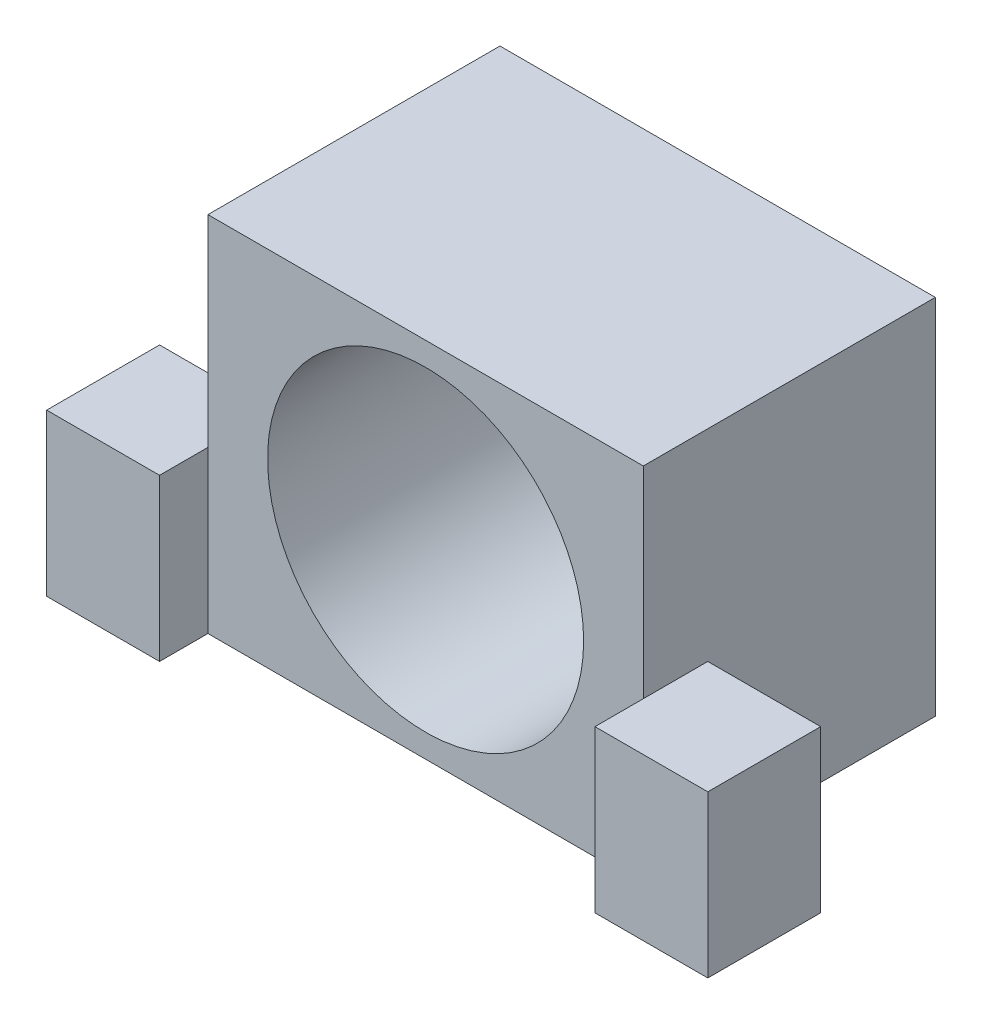
SolidWorks part; units mm, degrees
ref_plane "Front Plane" through (0, 0, 0) normal (0, 0, 1) x (1, 0, 0)
ref_plane "Top Plane" through (0, 0, 0) normal (0, 1, 0) x (1, 0, 0)
ref_plane "Right Plane" through (0, 0, 0) normal (1, 0, 0) x (0, 0, -1)
sketch "Sketch1" plane through (0, 0, 0) normal (0, 0, 1) x (1, 0, 0)
  line L0 (17.145, -14.2875) -> (-17.145, -14.2875)
  line L1 (-17.145, 14.2875) -> (17.145, 14.2875)
  line L2 (-17.145, 14.2875) -> (-17.145, -14.2875)
  line L3 (-17.145, 0) -> (17.145, 0) construction
  line L4 (17.145, 14.2875) -> (17.145, -14.2875)
  line L5 (0, 14.2875) -> (0, -14.2875) construction
  dimension "D2" = 34.29
  dimension "D3" = 28.575
extrude "Boss-Extrude1" add sketch "Sketch1" along normal blind 23
sketch "Sketch3" plane through (0, 0, 23) normal (0, 0, 1) x (1, 0, 0)
  circle A0 centre (0, 0) radius 12.446
  dimension "D1" = 24.892
extrude "Cut-Extrude1" cut sketch "Sketch3" against normal blind 21
sketch "Sketch5" plane through (0, 0, 2) normal (0, 0, 1) x (1, 0, 0)
  circle A0 centre (0, 8.5) radius 1.625
  circle A1 centre (-8.5, 0) radius 1.625
  circle A2 centre (8.5, 0) radius 1.625
  circle A3 centre (0, -8.5) radius 1.625
  circle A4 centre (0, 0) radius 8.5 construction
  circle A5 centre (0, 0) radius 3.75
  dimension "D1" = 3.25
  dimension "D2" = 17
  dimension "D3" = 7.5
extrude "Cut-Extrude2" cut sketch "Sketch5" against normal through all
sketch "Sketch7" plane through (0, 0, 23) normal (0, 0, 1) x (1, 0, 0)
  line L0 (0, 15.1888) -> (0, -15.3037) construction
  line L1 (-17.145, -1.5875) -> (-26.035, -1.5875)
  line L2 (-17.145, -1.5875) -> (-17.145, -14.2875)
  line L3 (-17.145, -14.2875) -> (-26.035, -14.2875)
  line L4 (-26.035, -1.5875) -> (-26.035, -14.2875)
  line L5 (17.145, -1.5875) -> (26.035, -1.5875)
  line L6 (17.145, -1.5875) -> (17.145, -14.2875)
  line L7 (17.145, -14.2875) -> (26.035, -14.2875)
  line L8 (26.035, -1.5875) -> (26.035, -14.2875)
  line L12 (-17.145, -14.2875) -> (17.145, -14.2875) construction
  dimension "D1" = 12.7
  dimension "D2" = 8.89
  dimension "D4" = 17.145
extrude "Boss-Extrude2" add sketch "Sketch7" along normal blind 3.81 and the other way blind 5.08
